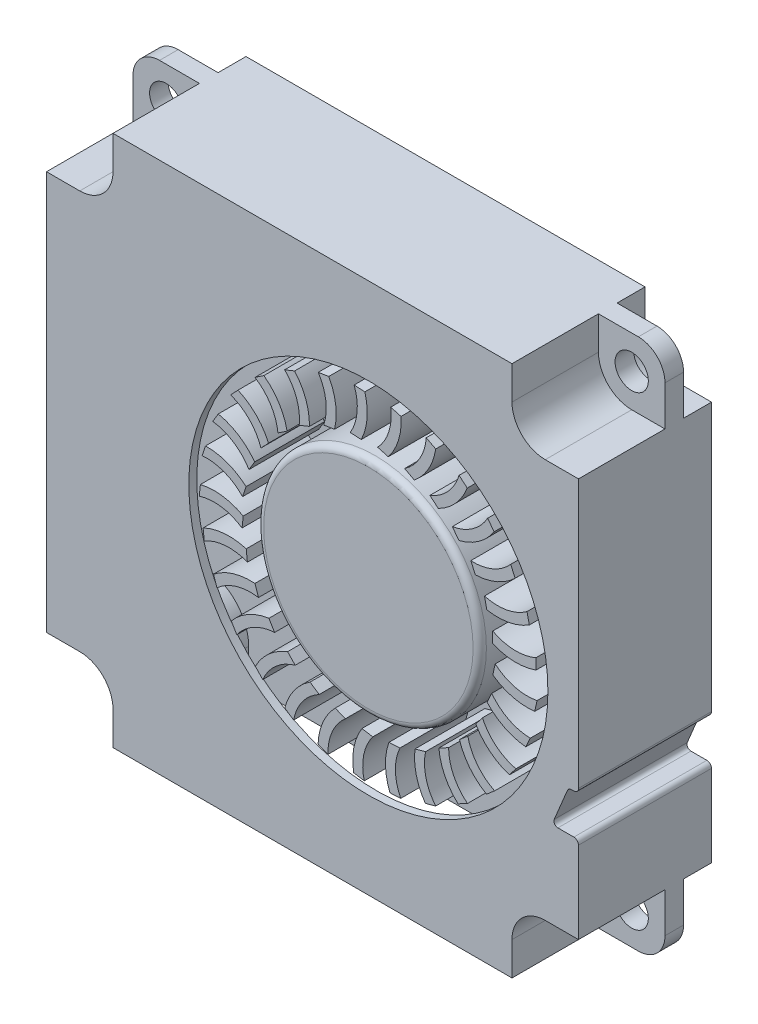
SolidWorks part; units mm, degrees
ref_plane "Front Plane" through (0, 0, 0) normal (0, 0, 1) x (1, 0, 0)
ref_plane "Top Plane" through (0, 0, 0) normal (0, 1, 0) x (1, 0, 0)
ref_plane "Right Plane" through (0, 0, 0) normal (1, 0, 0) x (0, 0, -1)
ref_plane "Plane3" through (0, 0, 25.289) normal (0, 0, 1) x (1, 0, 0)
sketch "Sketch35" plane through (0, 0, 25.289) normal (0, 0, 1) x (1, 0, 0)
  line L0 (41.5884, 7.4054) -> (41.5884, 47.4054)
  line L1 (41.5884, 47.4054) -> (1.5884, 47.4054)
  line L2 (1.5884, 47.4054) -> (1.5884, 7.4054)
  line L3 (1.5884, 7.4054) -> (41.5884, 7.4054)
extrude "Boss-Extrude31" add sketch "Sketch35" against normal blind 10 separate body
sketch "Sketch36" plane through (0, 7.4054, 0) normal (0, -1, 0) x (1, 0, 0)
  line L0 (35.5884, 24.689) -> (7.5884, 24.689)
  line L1 (7.5884, 24.689) -> (7.5884, 16.089)
  line L2 (7.5884, 16.089) -> (35.5884, 16.089)
  line L3 (35.5884, 16.089) -> (35.5884, 24.689)
extrude "Cut-Extrude1" cut sketch "Sketch36" against normal blind 39
ref_plane "Plane4" through (7.5884, 0, 0) normal (1, 0, 0) x (0, 0, -1)
sketch "Sketch41" plane through (7.5884, 0, 0) normal (1, 0, 0) x (0, 0, -1)
  line L0 (-24.689, 46.4054) -> (-24.689, 13.4054)
  line L1 (-24.689, 13.4054) -> (-16.089, 13.4054)
  line L2 (-16.089, 13.4054) -> (-16.089, 46.4054)
  line L3 (-16.089, 46.4054) -> (-24.689, 46.4054)
extrude "Cut-Extrude2" cut sketch "Sketch41" against normal blind 5
sketch "Sketch42" plane through (35.5884, 0, 0) normal (-1, 0, 0) x (0, 0, 1)
  line L0 (24.689, 13.4054) -> (24.689, 46.4054)
  line L1 (24.689, 46.4054) -> (16.089, 46.4054)
  line L2 (16.089, 46.4054) -> (16.089, 13.4054)
  line L3 (16.089, 13.4054) -> (24.689, 13.4054)
extrude "Cut-Extrude3" cut sketch "Sketch42" against normal blind 5
ref_plane "Plane5" through (0, 0, 24.689) normal (0, 0, -1) x (-1, 0, 0)
sketch "Sketch48" plane through (0, 0, 24.689) normal (0, 0, -1) x (-1, 0, 0)
  line L0 (-40.5884, 17.9054) -> (-40.5884, 22.825)
  line L1 (-39.8384, 22.1054) -> (-38.8384, 19.7054)
  line L2 (-40.0384, 17.9054) -> (-40.5884, 17.9054)
  arc A0 (-40.5884, 22.825) -> (-39.8384, 22.1054) centre (-41.0384, 21.6054) cw
  arc A1 (-38.8384, 19.7054) -> (-40.0384, 17.9054) centre (-40.0384, 19.2054) cw
extrude "Boss-Extrude32" add sketch "Sketch48" along normal blind 8.6
sketch "Sketch49" plane through (0, 0, 15.289) normal (0, 0, -1) x (-1, 0, 0)
  line L0 (-41.5884, 18.9054) -> (-40.0384, 18.9054)
  line L1 (-39.7615, 19.3207) -> (-40.8384, 21.9054)
  line L2 (-40.8384, 21.9054) -> (-41.5884, 21.9054)
  line L3 (-41.5884, 21.9054) -> (-41.5884, 18.9054)
  arc A0 (-40.0384, 18.9054) -> (-39.7615, 19.3207) centre (-40.0384, 19.2054) ccw
extrude "Cut-Extrude4" cut sketch "Sketch49" against normal through all
sketch "Sketch50" plane through (0, 0, 24.689) normal (0, 0, -1) x (-1, 0, 0)
  line L0 (-40.5884, 41.4054) -> (-40.5884, 46.4054)
  line L1 (-40.5884, 46.4054) -> (-35.5884, 46.4054)
  line L2 (-35.5884, 46.4054) -> (-35.5884, 41.4054)
  line L3 (-35.5884, 41.4054) -> (-40.5884, 41.4054)
extrude "Boss-Extrude33" add sketch "Sketch50" along normal blind 8.6
sketch "Sketch51" plane through (0, 0, 24.689) normal (0, 0, -1) x (-1, 0, 0)
  line L0 (-7.5884, 46.4054) -> (-2.5884, 46.4054)
  line L1 (-2.5884, 46.4054) -> (-2.5884, 41.4054)
  line L2 (-2.5884, 41.4054) -> (-7.5884, 41.4054)
  line L3 (-7.5884, 41.4054) -> (-7.5884, 46.4054)
extrude "Boss-Extrude34" add sketch "Sketch51" along normal blind 8.6
sketch "Sketch52" plane through (0, 0, 25.289) normal (0, 0, 1) x (1, 0, 0)
  line L0 (6.5884, 7.4054) -> (6.5884, 12.4054)
  line L1 (6.5884, 12.4054) -> (1.5884, 12.4054)
  line L2 (1.5884, 12.4054) -> (1.5884, 7.4054)
  line L3 (1.5884, 7.4054) -> (6.5884, 7.4054)
extrude "Cut-Extrude5" cut sketch "Sketch52" against normal blind 6.5
sketch "Sketch53" plane through (0, 0, 25.289) normal (0, 0, 1) x (1, 0, 0)
  line L0 (1.5884, 42.4054) -> (6.5884, 42.4054)
  line L1 (6.5884, 42.4054) -> (6.5884, 47.4054)
  line L2 (6.5884, 47.4054) -> (1.5884, 47.4054)
  line L3 (1.5884, 47.4054) -> (1.5884, 42.4054)
extrude "Cut-Extrude6" cut sketch "Sketch53" against normal blind 6.5
sketch "Sketch54" plane through (0, 0, 25.289) normal (0, 0, 1) x (1, 0, 0)
  line L0 (41.5884, 12.4054) -> (36.5884, 12.4054)
  line L1 (36.5884, 12.4054) -> (36.5884, 7.4054)
  line L2 (36.5884, 7.4054) -> (41.5884, 7.4054)
  line L3 (41.5884, 7.4054) -> (41.5884, 12.4054)
extrude "Cut-Extrude7" cut sketch "Sketch54" against normal blind 6.5
sketch "Sketch55" plane through (0, 0, 25.289) normal (0, 0, 1) x (1, 0, 0)
  line L0 (36.5884, 47.4054) -> (36.5884, 42.4054)
  line L1 (36.5884, 42.4054) -> (41.5884, 42.4054)
  line L2 (41.5884, 42.4054) -> (41.5884, 47.4054)
  line L3 (41.5884, 47.4054) -> (36.5884, 47.4054)
extrude "Cut-Extrude8" cut sketch "Sketch55" against normal blind 6.5
sketch "Sketch56" plane through (0, 0, 15.289) normal (0, 0, -1) x (-1, 0, 0)
  line L0 (-41.5884, 42.4054) -> (-36.5884, 42.4054)
  line L1 (-36.5884, 42.4054) -> (-36.5884, 47.4054)
  line L2 (-36.5884, 47.4054) -> (-41.5884, 47.4054)
  line L3 (-41.5884, 47.4054) -> (-41.5884, 42.4054)
extrude "Cut-Extrude9" cut sketch "Sketch56" against normal blind 2.1
sketch "Sketch57" plane through (0, 0, 15.289) normal (0, 0, -1) x (-1, 0, 0)
  line L0 (-36.5884, 7.4054) -> (-36.5884, 12.4054)
  line L1 (-36.5884, 12.4054) -> (-41.5884, 12.4054)
  line L2 (-41.5884, 12.4054) -> (-41.5884, 7.4054)
  line L3 (-41.5884, 7.4054) -> (-36.5884, 7.4054)
extrude "Cut-Extrude10" cut sketch "Sketch57" against normal blind 2.1
sketch "Sketch58" plane through (0, 0, 15.289) normal (0, 0, -1) x (-1, 0, 0)
  line L0 (-6.5884, 42.4054) -> (-1.5884, 42.4054)
  line L1 (-1.5884, 42.4054) -> (-1.5884, 47.4054)
  line L2 (-1.5884, 47.4054) -> (-6.5884, 47.4054)
  line L3 (-6.5884, 47.4054) -> (-6.5884, 42.4054)
extrude "Cut-Extrude11" cut sketch "Sketch58" against normal blind 2.1
sketch "Sketch59" plane through (0, 0, 15.289) normal (0, 0, -1) x (-1, 0, 0)
  line L0 (-6.5884, 12.4054) -> (-6.5884, 7.4054)
  line L1 (-6.5884, 7.4054) -> (-1.5884, 7.4054)
  line L2 (-1.5884, 7.4054) -> (-1.5884, 12.4054)
  line L3 (-1.5884, 12.4054) -> (-6.5884, 12.4054)
extrude "Cut-Extrude12" cut sketch "Sketch59" against normal blind 2.1
hole_wizard "Ø2.5 (2.5) Diameter Hole1" positions "Sketch61" profile "Sketch60" hole size "Ø2.5" standard "ANSI Metric"
sketch "Sketch61" plane through (0, 0, 18.789) normal (0, 0, 1) x (1, 0, 0)
  point P0 (4.0884, 44.9054)
  point P1 (39.0884, 9.9054)
sketch "Sketch60" plane through (4.0884, 44.9054, 18.789) normal (1, 0, 0) x (0, -1, 0)
  line L0 (0, 0) -> (0, 3.5)
  line L1 (0, 3.5) -> (1.25, 3.5)
  line L2 (1.25, 3.5) -> (1.25, 0)
  line L5 (1.25, 0) -> (0, 0)
  line L10 (0, 3.5) -> (-1.25, 3.5) construction
  line L11 (0, -6.35) -> (0, 107.95) construction
  dimension "Hole Dia." = 2.5
  dimension "Hole Depth" = 3.5
  dimension "Drill Angle" = 180
hole_wizard "M24 Clearance Hole1" positions "Sketch63" profile "Sketch62" hole size "M24" standard "ANSI Metric"
sketch "Sketch63" plane through (0, 0, 25.289) normal (0, 0, 1) x (1, 0, 0)
  point P0 (25.7884, 27.4054)
sketch "Sketch62" plane through (25.7884, 27.4054, 25.289) normal (1, 0, 0) x (0, -1, 0)
  line L0 (0, 0) -> (0, 0.6)
  line L1 (0, 0.6) -> (13.5, 0.6)
  line L2 (13.5, 0.6) -> (13.5, 0)
  line L5 (13.5, 0) -> (0, 0)
  line L11 (0, -6.35) -> (0, 107.95) construction
  dimension "Thru Hole Dia." = 27
  dimension "Thru Hole Depth" = 0.6
hole_wizard "Ø2.5 (2.5) Diameter Hole2" positions "Sketch65" profile "Sketch64" hole size "Ø2.5" standard "ANSI Metric"
sketch "Sketch65" plane through (0, 0, 17.389) normal (0, 0, -1) x (-1, 0, 0)
  point P0 (-4.0884, 9.9054)
  point P1 (-39.0884, 44.9054)
sketch "Sketch64" plane through (4.0884, 9.9054, 17.389) normal (1, 0, 0) x (0, 1, 0)
  line L0 (0, 0) -> (0, 7.9)
  line L1 (0, 7.9) -> (1.25, 7.9)
  line L2 (1.25, 7.9) -> (1.25, 0)
  line L5 (1.25, 0) -> (0, 0)
  line L10 (0, 7.9) -> (-1.25, 7.9) construction
  line L11 (0, -6.35) -> (0, 107.95) construction
  dimension "Hole Dia." = 2.5
  dimension "Hole Depth" = 7.9
  dimension "Drill Angle" = 180
fillet "Fillet2" radius 0.35 3 edges at (41.5884, 18.9054, 20.289) (40.8384, 21.9054, 20.289) (41.5884, 21.9054, 20.289)
fillet "Fillet3" radius 2 4 edges at (1.5884, 47.4054, 18.089) (41.5884, 47.4054, 18.089) (1.5884, 7.4054, 18.089) (41.5884, 7.4054, 18.089)
fillet "Fillet4" radius 2.5 8 edges at (6.5884, 12.4054, 22.039) (36.5884, 12.4054, 16.339) (36.5884, 42.4054, 16.339) (6.5884, 12.4054, 16.339) (6.5884, 42.4054, 16.339) (36.5884, 12.4054, 22.039) (6.5884, 42.4054, 22.039) (36.5884, 42.4054, 22.039)
fillet "Fillet5" radius 3.5 4 edges at (7.5884, 41.4054, 20.389) (7.5884, 13.4054, 20.389) (35.5884, 13.4054, 20.389) (35.5884, 41.4054, 20.389)
ref_plane "Plane6" through (0, 0, 20.039) normal (0, 0, 1) x (1, 0, 0)
sketch "Sketch72" plane through (0, 0, 20.039) normal (0, 0, 1) x (1, 0, 0)
  line L0 (38.3896, 28.3542) -> (38.3887, 29.1599)
  line L1 (37.891, 31.0409) -> (37.7169, 31.8275)
  line L2 (36.8265, 33.5576) -> (36.4874, 34.2884)
  line L3 (35.2459, 35.7866) -> (34.7576, 36.4275)
  line L4 (33.2231, 37.6237) -> (32.6084, 38.1447)
  line L5 (30.8526, 38.9831) -> (30.1403, 39.3597)
  line L6 (28.2453, 39.8011) -> (27.4688, 40.0157)
  line L7 (25.5232, 40.0394) -> (24.7186, 40.0821)
  line L8 (22.8134, 39.687) -> (22.0185, 39.5558)
  line L9 (20.2428, 38.7604) -> (19.4946, 38.4613)
  line L10 (17.9314, 37.3028) -> (17.2651, 36.8499)
  line L11 (15.9875, 35.3824) -> (15.4341, 34.7968)
  line L12 (14.5018, 33.089) -> (14.0872, 32.3981)
  line L13 (13.5439, 30.5298) -> (13.2875, 29.766)
  line L14 (13.1585, 27.8245) -> (13.0723, 27.0235)
  line L15 (13.3636, 25.0997) -> (13.4517, 24.2988)
  line L16 (14.1498, 22.4826) -> (14.4079, 21.7194)
  line L17 (15.4801, 20.0958) -> (15.8963, 19.4059)
  line L18 (17.2925, 18.0507) -> (17.8472, 17.4664)
  line L19 (19.5021, 16.443) -> (20.1694, 15.9916)
  line L20 (22.0056, 15.3479) -> (22.7544, 15.0506)
  line L21 (24.686, 14.8167) -> (25.4813, 14.6872)
  line L22 (27.418, 14.874) -> (28.2225, 14.9185)
  line L23 (30.0738, 15.5173) -> (30.8499, 15.7337)
  line L24 (32.5292, 16.7165) -> (33.2406, 17.0947)
  line L25 (34.6694, 18.4154) -> (35.2828, 18.9377)
  line L26 (36.3943, 20.5348) -> (36.8812, 21.1767)
  line L27 (37.6233, 22.9754) -> (37.9608, 23.707)
  line L28 (38.2989, 25.6231) -> (38.4712, 26.4102)
  arc A0 (36.2607, 26.6429) -> (36.2628, 28.1383) centre (25.7884, 27.4054) ccw
  arc A1 (36.2628, 28.1383) -> (38.3896, 28.3542) centre (36.8847, 32.5951) ccw
  arc A2 (38.3887, 29.1599) -> (36.1797, 28.9119) centre (36.8847, 32.5951) cw
  arc A3 (36.1797, 28.9119) -> (35.8603, 30.3728) centre (25.7884, 27.4054) ccw
  arc A4 (35.8603, 30.3728) -> (37.891, 31.0409) centre (35.5097, 34.8591) ccw
  arc A5 (37.7169, 31.8275) -> (35.6129, 31.1106) centre (35.5097, 34.8591) cw
  arc A6 (35.6129, 31.1106) -> (34.9869, 32.4686) centre (25.7884, 27.4054) ccw
  arc A7 (34.9869, 32.4686) -> (36.8265, 33.5576) centre (33.6801, 36.7747) ccw
  arc A8 (36.4874, 34.2884) -> (34.5867, 33.1359) centre (33.6801, 36.7747) cw
  arc A9 (34.5867, 33.1359) -> (33.6834, 34.3277) centre (25.7884, 27.4054) ccw
  arc A10 (33.6834, 34.3277) -> (35.2459, 35.7866) centre (31.4814, 38.2521) ccw
  arc A11 (34.7576, 36.4275) -> (33.1491, 34.8933) centre (31.4814, 38.2521) cw
  arc A12 (33.1491, 34.8933) -> (32.0108, 35.863) centre (25.7884, 27.4054) ccw
  arc A13 (32.0108, 35.863) -> (33.2231, 37.6237) centre (29.0166, 39.2223) ccw
  arc A14 (32.6084, 38.1447) -> (31.3673, 36.3006) centre (29.0166, 39.2223) cw
  arc A15 (31.3673, 36.3006) -> (30.0471, 37.0029) centre (25.7884, 27.4054) ccw
  arc A16 (30.0471, 37.0029) -> (30.8526, 38.9831) centre (26.4008, 39.64) ccw
  arc A17 (30.1403, 39.3597) -> (29.3247, 37.2919) centre (26.4008, 39.64) cw
  arc A18 (29.3247, 37.2919) -> (27.8844, 37.694) centre (25.7884, 27.4054) ccw
  arc A19 (27.8844, 37.694) -> (28.2453, 39.8011) centre (23.7564, 39.4856) ccw
  arc A20 (27.4688, 40.0157) -> (27.1167, 37.821) centre (23.7564, 39.4856) cw
  arc A21 (27.1167, 37.821) -> (25.6236, 37.9041) centre (25.7884, 27.4054) ccw
  arc A22 (25.6236, 37.9041) -> (25.5232, 40.0394) centre (21.207, 38.7664) ccw
  arc A23 (24.7186, 40.0821) -> (24.8466, 37.863) centre (21.207, 38.7664) cw
  arc A24 (24.8466, 37.863) -> (23.3705, 37.6232) centre (25.7884, 27.4054) ccw
  arc A25 (23.3705, 37.6232) -> (22.8134, 39.687) centre (18.8718, 37.5159) ccw
  arc A26 (22.0185, 39.5558) -> (22.6205, 37.4161) centre (18.8718, 37.5159) cw
  arc A27 (22.6205, 37.4161) -> (21.2305, 36.8645) centre (25.7884, 27.4054) ccw
  arc A28 (21.2305, 36.8645) -> (20.2428, 38.7604) centre (16.8601, 35.7927) ccw
  arc A29 (19.4946, 38.4613) -> (20.5425, 36.501) centre (16.8601, 35.7927) cw
  arc A30 (20.5425, 36.501) -> (19.3037, 35.6636) centre (25.7884, 27.4054) ccw
  arc A31 (19.3037, 35.6636) -> (17.9314, 37.3028) centre (15.2658, 33.6773) ccw
  arc A32 (17.2651, 36.8499) -> (18.7099, 35.1607) centre (15.2658, 33.6773) cw
  arc A33 (18.7099, 35.1607) -> (17.68, 34.0765) centre (25.7884, 27.4054) ccw
  arc A34 (17.68, 34.0765) -> (15.9875, 35.3824) centre (14.1635, 31.2686) ccw
  arc A35 (15.4341, 34.7968) -> (17.2082, 33.4577) centre (14.1635, 31.2686) cw
  arc A36 (17.2082, 33.4577) -> (16.4355, 32.1775) centre (25.7884, 27.4054) ccw
  arc A37 (16.4355, 32.1775) -> (14.5018, 33.089) centre (13.6048, 28.6793) ccw
  arc A38 (14.0872, 32.3981) -> (16.1077, 31.4717) centre (13.6048, 28.6793) cw
  arc A39 (16.1077, 31.4717) -> (15.6283, 30.0553) centre (25.7884, 27.4054) ccw
  arc A40 (15.6283, 30.0553) -> (13.5439, 30.5298) centre (13.6158, 26.0304) ccw
  arc A41 (13.2875, 29.766) -> (15.4599, 29.2956) centre (13.6158, 26.0304) cw
  arc A42 (15.4599, 29.2956) -> (15.2961, 27.8092) centre (25.7884, 27.4054) ccw
  arc A43 (15.2961, 27.8092) -> (13.1585, 27.8245) centre (14.196, 23.4458) ccw
  arc A44 (13.0723, 27.0235) -> (15.295, 27.0311) centre (14.196, 23.4458) cw
  arc A45 (15.295, 27.0311) -> (15.4546, 25.5443) centre (25.7884, 27.4054) ccw
  arc A46 (15.4546, 25.5443) -> (13.3636, 25.0997) centre (15.3182, 21.0463) ccw
  arc A47 (13.4517, 24.2988) -> (15.6208, 24.7841) centre (15.3182, 21.0463) cw
  arc A48 (15.6208, 24.7841) -> (16.0963, 23.3663) centre (25.7884, 27.4054) ccw
  arc A49 (16.0963, 23.3663) -> (14.1498, 22.4826) centre (16.93, 18.9442) ccw
  arc A50 (14.4079, 21.7194) -> (16.422, 22.6596) centre (16.93, 18.9442) cw
  arc A51 (16.422, 22.6596) -> (17.1912, 21.3772) centre (25.7884, 27.4054) ccw
  arc A52 (17.1912, 21.3772) -> (15.4801, 20.0958) centre (18.956, 17.2377) ccw
  arc A53 (15.8963, 19.4059) -> (17.6612, 20.7571) centre (18.956, 17.2377) cw
  arc A54 (17.6612, 20.7571) -> (18.688, 19.67) centre (25.7884, 27.4054) ccw
  arc A55 (18.688, 19.67) -> (17.2925, 18.0507) centre (21.3014, 16.0067) ccw
  arc A56 (17.8472, 17.4664) -> (19.2804, 19.1654) centre (21.3014, 16.0067) cw
  arc A57 (19.2804, 19.1654) -> (20.5169, 18.3245) centre (25.7884, 27.4054) ccw
  arc A58 (20.5169, 18.3245) -> (19.5021, 16.443) centre (23.8567, 15.3086) ccw
  arc A59 (20.1694, 15.9916) -> (21.2039, 17.9591) centre (23.8567, 15.3086) cw
  arc A60 (21.2039, 17.9591) -> (22.5923, 17.4036) centre (25.7884, 27.4054) ccw
  arc A61 (22.5923, 17.4036) -> (22.0056, 15.3479) centre (26.5023, 15.1762) ccw
  arc A62 (22.7544, 15.0506) -> (23.3417, 17.1944) centre (26.5023, 15.1762) cw
  arc A63 (23.3417, 17.1944) -> (24.8171, 16.9504) centre (25.7884, 27.4054) ccw
  arc A64 (24.8171, 16.9504) -> (24.686, 14.8167) centre (29.1145, 15.6156) ccw
  arc A65 (25.4813, 14.6872) -> (25.594, 16.9072) centre (29.1145, 15.6156) cw
  arc A66 (25.594, 16.9072) -> (27.0873, 16.986) centre (25.7884, 27.4054) ccw
  arc A67 (27.0873, 16.986) -> (27.418, 14.874) centre (31.5712, 16.6062) ccw
  arc A68 (28.2225, 14.9185) -> (27.8553, 17.1108) centre (31.5712, 16.6062) cw
  arc A69 (27.8553, 17.1108) -> (29.2968, 17.5088) centre (25.7884, 27.4054) ccw
  arc A70 (29.2968, 17.5088) -> (30.0738, 15.5173) centre (33.7575, 18.1019) ccw
  arc A71 (30.8499, 15.7337) -> (30.02, 17.7958) centre (33.7575, 18.1019) cw
  arc A72 (30.02, 17.7958) -> (31.3422, 18.4944) centre (25.7884, 27.4054) ccw
  arc A73 (31.3422, 18.4944) -> (32.5292, 16.7165) centre (35.5712, 20.0325) ccw
  arc A74 (33.2406, 17.0947) -> (31.9869, 18.9302) centre (35.5712, 20.0325) cw
  arc A75 (31.9869, 18.9302) -> (33.128, 19.8967) centre (25.7884, 27.4054) ccw
  arc A76 (33.128, 19.8967) -> (34.6694, 18.4154) centre (36.9274, 22.3079) ccw
  arc A77 (35.2828, 18.9377) -> (33.6639, 20.4608) centre (36.9274, 22.3079) cw
  arc A78 (33.6639, 20.4608) -> (34.5705, 21.65) centre (25.7884, 27.4054) ccw
  arc A79 (34.5705, 21.65) -> (36.3943, 20.5348) centre (37.7628, 24.8216) ccw
  arc A80 (36.8812, 21.1767) -> (34.9726, 22.3162) centre (37.7628, 24.8216) cw
  arc A81 (34.9726, 22.3162) -> (35.6024, 23.6724) centre (25.7884, 27.4054) ccw
  arc A82 (35.6024, 23.6724) -> (37.6233, 22.9754) centre (38.0383, 27.4562) ccw
  arc A83 (37.9608, 23.707) -> (35.8519, 24.4095) centre (38.0383, 27.4562) cw
  arc A84 (35.8519, 24.4095) -> (36.1754, 25.8695) centre (25.7884, 27.4054) ccw
  arc A85 (36.1754, 25.8695) -> (38.2989, 25.6231) centre (37.7409, 30.0884) ccw
  arc A86 (38.4712, 26.4102) -> (36.2607, 26.6429) centre (37.7409, 30.0884) cw
extrude "Boss-Extrude35" add sketch "Sketch72" against normal blind 2 separate body
sketch "Sketch73" plane through (0, 0, 20.039) normal (0, 0, 1) x (1, 0, 0)
  line L0 (38.3887, 29.1599) -> (38.3896, 28.3542)
  line L1 (35.1395, 28.4473) -> (35.1385, 29.2765)
  arc A0 (35.1385, 29.2765) -> (38.3887, 29.1599) centre (36.8847, 32.5951) ccw
  arc A1 (38.3896, 28.3542) -> (35.1395, 28.4473) centre (36.8847, 32.5951) cw
extrude "Boss-Extrude36" add sketch "Sketch73" along normal blind 5.25
sketch "Sketch74" plane through (0, 0, 20.039) normal (0, 0, 1) x (1, 0, 0)
  line L0 (38.4712, 26.4102) -> (38.2989, 25.6231)
  line L1 (35.1448, 26.4127) -> (35.3222, 27.2227)
  arc A0 (35.3222, 27.2227) -> (38.4712, 26.4102) centre (37.7409, 30.0884) ccw
  arc A1 (38.2989, 25.6231) -> (35.1448, 26.4127) centre (37.7409, 30.0884) cw
extrude "Boss-Extrude37" add sketch "Sketch74" along normal blind 5.25
sketch "Sketch75" plane through (0, 0, 20.039) normal (0, 0, 1) x (1, 0, 0)
  line L0 (37.9608, 23.707) -> (37.6233, 22.9754)
  line L1 (34.7127, 24.4246) -> (35.06, 25.1775)
  arc A0 (35.06, 25.1775) -> (37.9608, 23.707) centre (38.0383, 27.4562) ccw
  arc A1 (37.6233, 22.9754) -> (34.7127, 24.4246) centre (38.0383, 27.4562) cw
extrude "Boss-Extrude38" add sketch "Sketch75" along normal blind 5.25
sketch "Sketch76" plane through (0, 0, 20.039) normal (0, 0, 1) x (1, 0, 0)
  line L0 (36.8812, 21.1767) -> (36.3943, 20.5348)
  line L1 (33.8633, 22.5758) -> (34.3643, 23.2365)
  arc A0 (34.3643, 23.2365) -> (36.8812, 21.1767) centre (37.7628, 24.8216) ccw
  arc A1 (36.3943, 20.5348) -> (33.8633, 22.5758) centre (37.7628, 24.8216) cw
extrude "Boss-Extrude39" add sketch "Sketch76" along normal blind 5.25
sketch "Sketch77" plane through (0, 0, 20.039) normal (0, 0, 1) x (1, 0, 0)
  line L0 (35.2828, 18.9377) -> (34.6694, 18.4154)
  line L1 (32.6363, 20.9529) -> (33.2676, 21.4904)
  arc A0 (33.2676, 21.4904) -> (35.2828, 18.9377) centre (36.9274, 22.3079) ccw
  arc A1 (34.6694, 18.4154) -> (32.6363, 20.9529) centre (36.9274, 22.3079) cw
extrude "Boss-Extrude40" add sketch "Sketch77" along normal blind 5.25
sketch "Sketch78" plane through (0, 0, 20.039) normal (0, 0, 1) x (1, 0, 0)
  line L0 (33.2406, 17.0947) -> (32.5292, 16.7165)
  line L1 (31.0891, 19.6316) -> (31.8212, 20.0208)
  arc A0 (31.8212, 20.0208) -> (33.2406, 17.0947) centre (35.5712, 20.0325) ccw
  arc A1 (32.5292, 16.7165) -> (31.0891, 19.6316) centre (35.5712, 20.0325) cw
extrude "Boss-Extrude41" add sketch "Sketch78" along normal blind 5.25
sketch "Sketch79" plane through (0, 0, 20.039) normal (0, 0, 1) x (1, 0, 0)
  line L0 (30.8499, 15.7337) -> (30.0738, 15.5173)
  line L1 (29.294, 18.6739) -> (30.0927, 18.8966)
  arc A0 (30.0927, 18.8966) -> (30.8499, 15.7337) centre (33.7575, 18.1019) ccw
  arc A1 (30.0738, 15.5173) -> (29.294, 18.6739) centre (33.7575, 18.1019) cw
extrude "Boss-Extrude42" add sketch "Sketch79" along normal blind 5.25
sketch "Sketch80" plane through (0, 0, 20.039) normal (0, 0, 1) x (1, 0, 0)
  line L0 (28.2225, 14.9185) -> (27.418, 14.874)
  line L1 (27.3351, 18.1244) -> (28.1629, 18.1702)
  arc A0 (28.1629, 18.1702) -> (28.2225, 14.9185) centre (31.5712, 16.6062) ccw
  arc A1 (27.418, 14.874) -> (27.3351, 18.1244) centre (31.5712, 16.6062) cw
extrude "Boss-Extrude43" add sketch "Sketch80" along normal blind 5.25
sketch "Sketch81" plane through (0, 0, 20.039) normal (0, 0, 1) x (1, 0, 0)
  line L0 (25.4813, 14.6872) -> (24.686, 14.8167)
  line L1 (25.3038, 18.0089) -> (26.1222, 17.8757)
  arc A0 (26.1222, 17.8757) -> (25.4813, 14.6872) centre (29.1145, 15.6156) ccw
  arc A1 (24.686, 14.8167) -> (25.3038, 18.0089) centre (29.1145, 15.6156) cw
extrude "Boss-Extrude44" add sketch "Sketch81" along normal blind 5.25
sketch "Sketch82" plane through (0, 0, 20.039) normal (0, 0, 1) x (1, 0, 0)
  line L0 (22.7544, 15.0506) -> (22.0056, 15.3479)
  line L1 (23.2951, 18.3327) -> (24.0657, 18.0267)
  arc A0 (24.0657, 18.0267) -> (22.7544, 15.0506) centre (26.5023, 15.1762) ccw
  arc A1 (22.0056, 15.3479) -> (23.2951, 18.3327) centre (26.5023, 15.1762) cw
extrude "Boss-Extrude45" add sketch "Sketch82" along normal blind 5.25
sketch "Sketch83" plane through (0, 0, 20.039) normal (0, 0, 1) x (1, 0, 0)
  line L0 (20.1694, 15.9916) -> (19.5021, 16.443)
  line L1 (21.4031, 19.0808) -> (22.0899, 18.6163)
  arc A0 (22.0899, 18.6163) -> (20.1694, 15.9916) centre (23.8567, 15.3086) ccw
  arc A1 (19.5021, 16.443) -> (21.4031, 19.0808) centre (23.8567, 15.3086) cw
extrude "Boss-Extrude46" add sketch "Sketch83" along normal blind 5.25
sketch "Sketch84" plane through (0, 0, 20.039) normal (0, 0, 1) x (1, 0, 0)
  line L0 (17.8472, 17.4664) -> (17.2925, 18.0507)
  line L1 (19.7161, 20.2182) -> (20.287, 19.6168)
  arc A0 (20.287, 19.6168) -> (17.8472, 17.4664) centre (21.3014, 16.0067) ccw
  arc A1 (17.2925, 18.0507) -> (19.7161, 20.2182) centre (21.3014, 16.0067) cw
extrude "Boss-Extrude47" add sketch "Sketch84" along normal blind 5.25
sketch "Sketch85" plane through (0, 0, 20.039) normal (0, 0, 1) x (1, 0, 0)
  line L0 (15.8963, 19.4059) -> (15.4801, 20.0958)
  line L1 (18.313, 21.6916) -> (18.7413, 20.9816)
  arc A0 (18.7413, 20.9816) -> (15.8963, 19.4059) centre (18.956, 17.2377) ccw
  arc A1 (15.4801, 20.0958) -> (18.313, 21.6916) centre (18.956, 17.2377) cw
extrude "Boss-Extrude48" add sketch "Sketch85" along normal blind 5.25
sketch "Sketch86" plane through (0, 0, 20.039) normal (0, 0, 1) x (1, 0, 0)
  line L0 (14.4079, 21.7194) -> (14.1498, 22.4826)
  line L1 (17.2595, 23.4321) -> (17.5251, 22.6467)
  arc A0 (17.5251, 22.6467) -> (14.4079, 21.7194) centre (16.93, 18.9442) ccw
  arc A1 (14.1498, 22.4826) -> (17.2595, 23.4321) centre (16.93, 18.9442) cw
extrude "Boss-Extrude49" add sketch "Sketch86" along normal blind 5.25
sketch "Sketch87" plane through (0, 0, 20.039) normal (0, 0, 1) x (1, 0, 0)
  line L0 (13.4517, 24.2988) -> (13.3636, 25.0997)
  line L1 (16.6048, 25.3585) -> (16.6953, 24.5343)
  arc A0 (16.6953, 24.5343) -> (13.4517, 24.2988) centre (15.3182, 21.0463) ccw
  arc A1 (13.3636, 25.0997) -> (16.6048, 25.3585) centre (15.3182, 21.0463) cw
extrude "Boss-Extrude50" add sketch "Sketch87" along normal blind 5.25
sketch "Sketch88" plane through (0, 0, 20.039) normal (0, 0, 1) x (1, 0, 0)
  line L0 (13.0723, 27.0235) -> (13.1585, 27.8245)
  line L1 (16.3794, 27.3805) -> (16.2907, 26.5561)
  arc A0 (16.2907, 26.5561) -> (13.0723, 27.0235) centre (14.196, 23.4458) ccw
  arc A1 (13.1585, 27.8245) -> (16.3794, 27.3805) centre (14.196, 23.4458) cw
extrude "Boss-Extrude51" add sketch "Sketch88" along normal blind 5.25
sketch "Sketch89" plane through (0, 0, 20.039) normal (0, 0, 1) x (1, 0, 0)
  line L0 (13.2875, 29.766) -> (13.5439, 30.5298)
  line L1 (16.5941, 29.4038) -> (16.3302, 28.6177)
  arc A0 (16.3302, 28.6177) -> (13.2875, 29.766) centre (13.6158, 26.0304) ccw
  arc A1 (13.5439, 30.5298) -> (16.5941, 29.4038) centre (13.6158, 26.0304) cw
extrude "Boss-Extrude52" add sketch "Sketch89" along normal blind 5.25
sketch "Sketch90" plane through (0, 0, 20.039) normal (0, 0, 1) x (1, 0, 0)
  line L0 (14.0872, 32.3981) -> (14.5018, 33.089)
  line L1 (17.2386, 31.3335) -> (16.812, 30.6226)
  arc A0 (16.812, 30.6226) -> (14.0872, 32.3981) centre (13.6048, 28.6793) ccw
  arc A1 (14.5018, 33.089) -> (17.2386, 31.3335) centre (13.6048, 28.6793) cw
extrude "Boss-Extrude53" add sketch "Sketch90" along normal blind 5.25
sketch "Sketch91" plane through (0, 0, 20.039) normal (0, 0, 1) x (1, 0, 0)
  line L0 (15.4341, 34.7968) -> (15.9875, 35.3824)
  line L1 (18.283, 33.0796) -> (17.7135, 32.477)
  arc A0 (17.7135, 32.477) -> (15.4341, 34.7968) centre (14.1635, 31.2686) ccw
  arc A1 (15.9875, 35.3824) -> (18.283, 33.0796) centre (14.1635, 31.2686) cw
extrude "Boss-Extrude54" add sketch "Sketch91" along normal blind 5.25
sketch "Sketch92" plane through (0, 0, 20.039) normal (0, 0, 1) x (1, 0, 0)
  line L0 (17.2651, 36.8499) -> (17.9314, 37.3028)
  line L1 (19.6783, 34.5604) -> (18.9925, 34.0943)
  arc A0 (18.9925, 34.0943) -> (17.2651, 36.8499) centre (15.2658, 33.6773) ccw
  arc A1 (17.9314, 37.3028) -> (19.6783, 34.5604) centre (15.2658, 33.6773) cw
extrude "Boss-Extrude55" add sketch "Sketch92" along normal blind 5.25
sketch "Sketch93" plane through (0, 0, 20.039) normal (0, 0, 1) x (1, 0, 0)
  line L0 (19.4946, 38.4613) -> (20.2428, 38.7604)
  line L1 (21.3592, 35.7066) -> (20.5893, 35.3988)
  arc A0 (20.5893, 35.3988) -> (19.4946, 38.4613) centre (16.8601, 35.7927) ccw
  arc A1 (20.2428, 38.7604) -> (21.3592, 35.7066) centre (16.8601, 35.7927) cw
extrude "Boss-Extrude56" add sketch "Sketch93" along normal blind 5.25
sketch "Sketch94" plane through (0, 0, 20.039) normal (0, 0, 1) x (1, 0, 0)
  line L0 (37.7169, 31.8275) -> (37.891, 31.0409)
  line L1 (34.6969, 30.4332) -> (34.5177, 31.2427)
  arc A0 (34.5177, 31.2427) -> (37.7169, 31.8275) centre (35.5097, 34.8591) ccw
  arc A1 (37.891, 31.0409) -> (34.6969, 30.4332) centre (35.5097, 34.8591) cw
extrude "Boss-Extrude57" add sketch "Sketch94" along normal blind 5.25
sketch "Sketch95" plane through (0, 0, 20.039) normal (0, 0, 1) x (1, 0, 0)
  line L0 (36.4874, 34.2884) -> (36.8265, 33.5576)
  line L1 (33.8377, 32.2774) -> (33.4887, 33.0295)
  arc A0 (33.4887, 33.0295) -> (36.4874, 34.2884) centre (33.6801, 36.7747) ccw
  arc A1 (36.8265, 33.5576) -> (33.8377, 32.2774) centre (33.6801, 36.7747) cw
extrude "Boss-Extrude58" add sketch "Sketch95" along normal blind 5.25
sketch "Sketch96" plane through (0, 0, 20.039) normal (0, 0, 1) x (1, 0, 0)
  line L0 (34.7576, 36.4275) -> (35.2459, 35.7866)
  line L1 (32.6022, 33.8939) -> (32.0996, 34.5534)
  arc A0 (32.0996, 34.5534) -> (34.7576, 36.4275) centre (31.4814, 38.2521) ccw
  arc A1 (35.2459, 35.7866) -> (32.6022, 33.8939) centre (31.4814, 38.2521) cw
extrude "Boss-Extrude59" add sketch "Sketch96" along normal blind 5.25
sketch "Sketch97" plane through (0, 0, 20.039) normal (0, 0, 1) x (1, 0, 0)
  line L0 (32.6084, 38.1447) -> (33.2231, 37.6237)
  line L1 (31.048, 35.2069) -> (30.4154, 35.743)
  arc A0 (30.4154, 35.743) -> (32.6084, 38.1447) centre (29.0166, 39.2223) ccw
  arc A1 (33.2231, 37.6237) -> (31.048, 35.2069) centre (29.0166, 39.2223) cw
extrude "Boss-Extrude60" add sketch "Sketch97" along normal blind 5.25
sketch "Sketch98" plane through (0, 0, 20.039) normal (0, 0, 1) x (1, 0, 0)
  line L0 (30.1403, 39.3597) -> (30.8526, 38.9831)
  line L1 (29.2479, 36.1552) -> (28.5149, 36.5428)
  arc A0 (28.5149, 36.5428) -> (30.1403, 39.3597) centre (26.4008, 39.64) ccw
  arc A1 (30.8526, 38.9831) -> (29.2479, 36.1552) centre (26.4008, 39.64) cw
extrude "Boss-Extrude61" add sketch "Sketch98" along normal blind 5.25
sketch "Sketch99" plane through (0, 0, 20.039) normal (0, 0, 1) x (1, 0, 0)
  line L0 (27.4688, 40.0157) -> (28.2453, 39.8011)
  line L1 (27.2861, 36.6943) -> (26.4869, 36.9153)
  arc A0 (26.4869, 36.9153) -> (27.4688, 40.0157) centre (23.7564, 39.4856) ccw
  arc A1 (28.2453, 39.8011) -> (27.2861, 36.6943) centre (23.7564, 39.4856) cw
extrude "Boss-Extrude62" add sketch "Sketch99" along normal blind 5.25
sketch "Sketch100" plane through (0, 0, 20.039) normal (0, 0, 1) x (1, 0, 0)
  line L0 (24.7186, 40.0821) -> (25.5232, 40.0394)
  line L1 (25.2542, 36.7991) -> (24.4262, 36.8431)
  arc A0 (24.4262, 36.8431) -> (24.7186, 40.0821) centre (21.207, 38.7664) ccw
  arc A1 (25.5232, 40.0394) -> (25.2542, 36.7991) centre (21.207, 38.7664) cw
extrude "Boss-Extrude63" add sketch "Sketch100" along normal blind 5.25
sketch "Sketch101" plane through (0, 0, 20.039) normal (0, 0, 1) x (1, 0, 0)
  line L0 (22.0185, 39.5558) -> (22.8134, 39.687)
  line L1 (23.2473, 36.4647) -> (22.4292, 36.3296)
  arc A0 (22.4292, 36.3296) -> (22.0185, 39.5558) centre (18.8718, 37.5159) ccw
  arc A1 (22.8134, 39.687) -> (23.2473, 36.4647) centre (18.8718, 37.5159) cw
extrude "Boss-Extrude64" add sketch "Sketch101" along normal blind 5.25
ref_plane "Plane7" through (0, 27.4054, 0) normal (0, -1, 0) x (-1, 0, 0)
sketch "Sketch109" plane through (0, 27.4054, 0) normal (0, -1, 0) x (-1, 0, 0)
  line L0 (-34.1634, -25.289) -> (-25.7884, -25.289)
  line L1 (-25.7884, -25.289) -> (-25.7884, -20.039)
  line L2 (-25.7884, -20.039) -> (-34.1634, -20.039)
  line L3 (-34.1634, -20.039) -> (-34.1634, -25.289)
  line L4 (-25.7884, -25.289) -> (-25.7884, -20.039) construction
revolve "Revolve2" add sketch "Sketch109" angle 360 about L4
fillet "Fillet6" radius 0.5 1 edges at (17.4134, 27.4054, 25.289)
